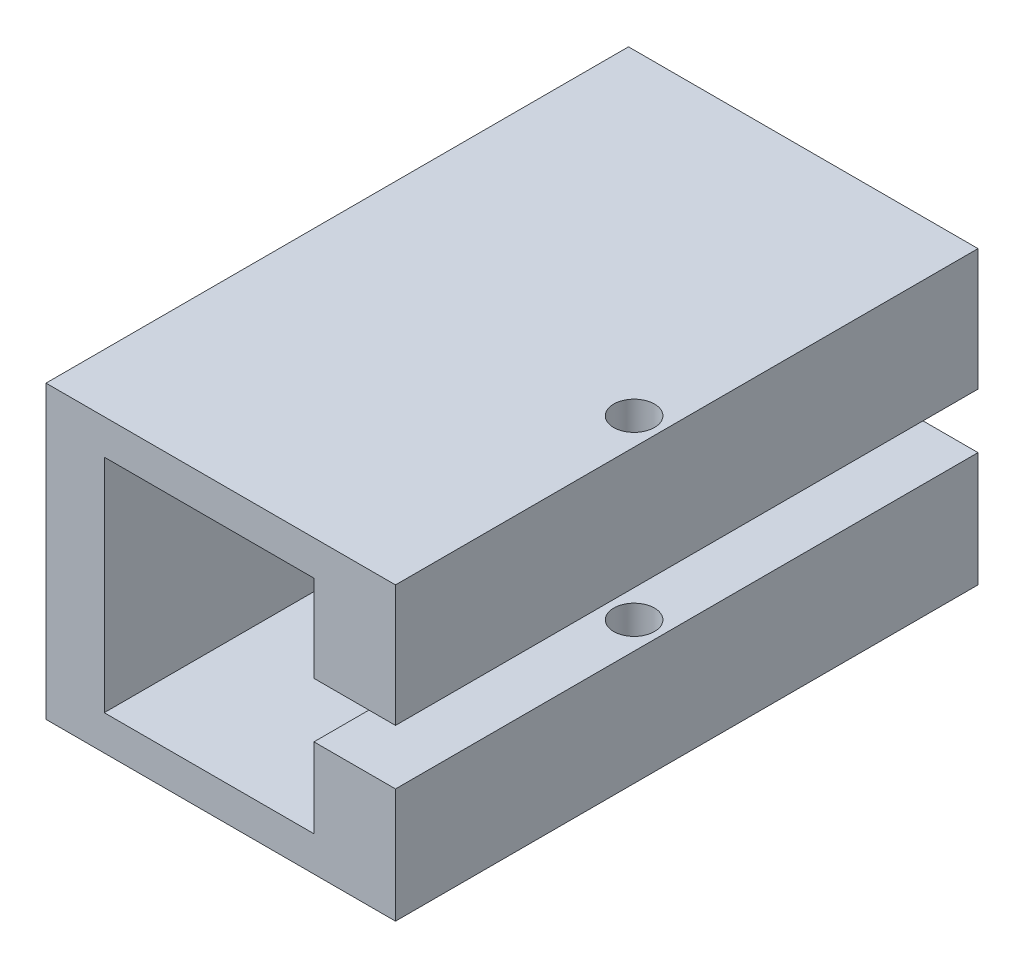
SolidWorks part; units mm, degrees
ref_plane "Front Plane" through (0, 0, 0) normal (0, 0, 1) x (1, 0, 0)
ref_plane "Top Plane" through (0, 0, 0) normal (0, 1, 0) x (1, 0, 0)
ref_plane "Right Plane" through (0, 0, 0) normal (1, 0, 0) x (0, 0, -1)
sketch "Sketch1" plane through (0, 0, 0) normal (0, 0, 1) x (1, 0, 0)
  line L2 (0, 0) -> (0, 25)
  line L11 (0, 25) -> (30, 25)
  line L17 (30, 0) -> (0, 0)
  line L19 (5, 22) -> (5, 3)
  line L21 (30, 25) -> (30, 14.5534)
  line L22 (30, 14.5534) -> (23, 14.5534)
  line L23 (23, 14.5534) -> (23, 22)
  line L24 (23, 22) -> (5, 22)
  line L25 (5, 3) -> (23, 3)
  line L26 (23, 3) -> (23, 9.8332)
  line L27 (23, 9.8332) -> (30, 9.8332)
  line L28 (30, 9.8332) -> (30, 0)
  dimension "D1" = 25
  dimension "D2" = 30
  dimension "D3" = 30
  dimension "D4" = 18
  dimension "D6" = 19
extrude "Boss-Extrude1" add sketch "Sketch1" along normal blind 50
sketch "Sketch3" plane through (0, 0, 0) normal (-1, 0, 0) x (0, 0, 1)
  line L0 (4.9195, 16.0567) -> (21.9195, 16.0567)
  line L1 (21.9195, 16.0567) -> (21.9195, 24.0567)
  line L2 (21.9195, 24.0567) -> (27.9195, 24.0567)
  line L3 (27.9195, 24.0567) -> (27.9195, 16.0567)
  line L4 (27.9195, 16.0567) -> (42.9195, 16.0567)
  line L5 (42.9195, 16.0567) -> (42.9195, 9.0567)
  line L6 (42.9195, 9.0567) -> (27.9195, 9.0567)
  line L7 (27.9195, 9.0567) -> (27.9195, 1.0567)
  line L8 (27.9195, 1.0567) -> (21.9195, 1.0567)
  line L9 (21.9195, 1.0567) -> (21.9195, 9.0567)
  line L10 (21.9195, 9.0567) -> (4.9195, 9.0567)
  line L13 (4.9195, 16.0567) -> (4.9195, 9.0567)
  circle A0 centre (40.25, 12.5203) radius 0.55
  circle A1 centre (8.9802, 12.5203) radius 0.55
  dimension "D12" = 1.1
  dimension "D13" = 1.1
  dimension "D1" = 7
  dimension "D2" = 8
  dimension "D3" = 8
  dimension "D4" = 7
  dimension "D5" = 8
  dimension "D6" = 6
  dimension "D7" = 17
  dimension "D8" = 17
  dimension "D9" = 15
  dimension "D10" = 15
  dimension "D11" = 6
extrude "Cut-Extrude1" cut sketch "Sketch3" against normal blind 3
sketch "Sketch4" plane through (0, 25, 0) normal (0, 1, 0) x (1, 0, 0)
  circle A0 centre (27.6682, -27.1887) radius 1.75
  dimension "D1" = 3.5
extrude "Cut-Extrude2" cut sketch "Sketch4" against normal blind 26
